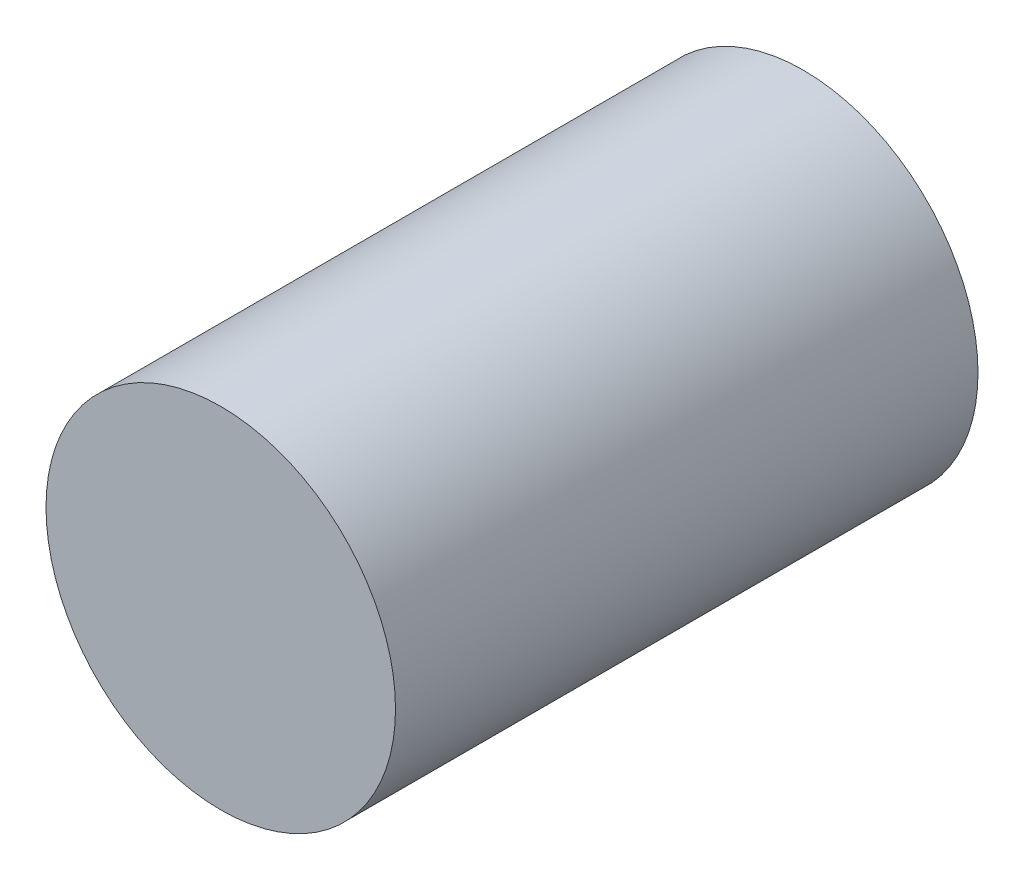
SolidWorks part; units mm, degrees
ref_plane "Front Plane" through (0, 0, 0) normal (0, 0, 1) x (1, 0, 0)
ref_plane "Top Plane" through (0, 0, 0) normal (0, 1, 0) x (1, 0, 0)
ref_plane "Right Plane" through (0, 0, 0) normal (1, 0, 0) x (0, 0, -1)
sketch "Sketch1" plane through (0, 0, 0) normal (0, 0, 1) x (1, 0, 0)
  circle A0 centre (0, 0) radius 3
  dimension "D1" = 6
extrude "Boss-Extrude1" add sketch "Sketch1" along normal blind 10
